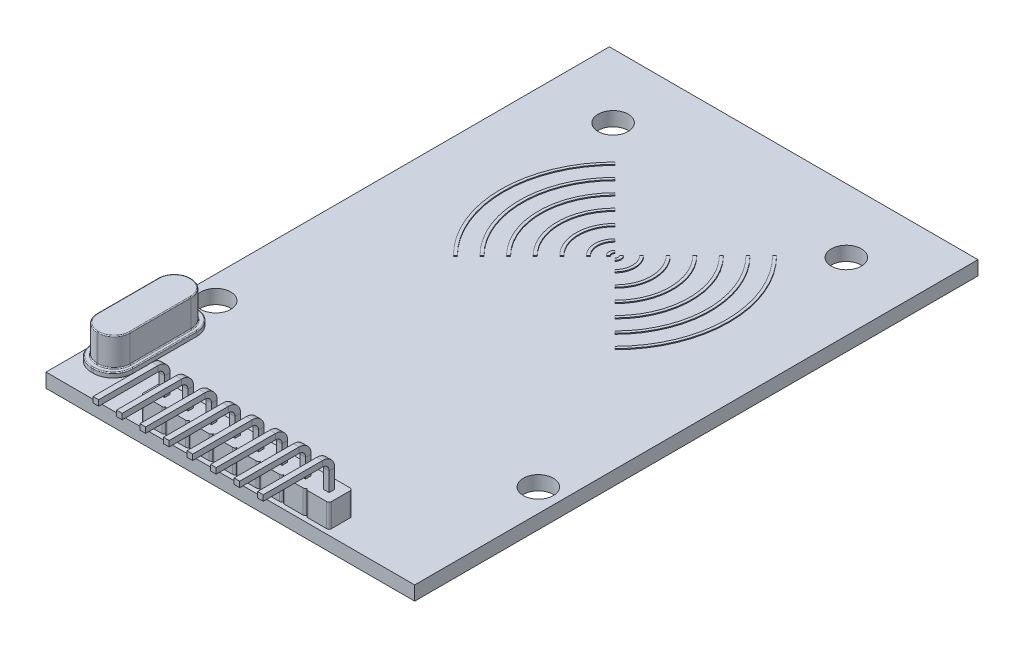
SolidWorks part; units mm, degrees
ref_plane "Front Plane" through (0, 0, 0) normal (0, 0, 1) x (1, 0, 0)
ref_plane "Top Plane" through (0, 0, 0) normal (0, 1, 0) x (1, 0, 0)
ref_plane "Right Plane" through (0, 0, 0) normal (1, 0, 0) x (0, 0, -1)
sketch "Sketch1" plane through (0, 0, 0) normal (0, 1, 0) x (1, 0, 0)
  line L1 (-19.6, 29.95) -> (19.6, 29.95)
  line L2 (-19.6, 29.95) -> (-19.6, -29.95)
  line L3 (-19.6, -29.95) -> (19.6, -29.95)
  line L4 (19.6, 29.95) -> (19.6, -29.95)
  line L5 (-19.6, 29.95) -> (19.6, -29.95) construction
  line L6 (-19.6, -29.95) -> (19.6, 29.95) construction
  point P0 (0, 0)
  dimension "D1" = 39.2
  dimension "D2" = 59.9
extrude "Boss-Extrude1" add sketch "Sketch1" along normal blind 1.5
sketch "Sketch3" plane through (0, 1.5, 0) normal (0, 1, 0) x (1, 0, 0)
  line L1 (-19.6, 29.95) -> (-19.6, -29.95) construction
  line L2 (19.6, 29.95) -> (-19.6, 29.95) construction
  line L5 (-19.6, -29.95) -> (19.6, -29.95) construction
  circle A0 centre (12.4, 23.15) radius 1.6
  circle A1 centre (-12.4, 23.15) radius 1.6
  circle A2 centre (17.15, -14.35) radius 1.6
  circle A3 centre (-17.15, -14.35) radius 1.6
  point P14 (0, 0)
  point P15 (0, 0)
  point P16 (0, 0)
  dimension "D1" = 3.2
  dimension "D2" = 24.8
  dimension "D3" = 6.8
  dimension "D4" = 7.2
  dimension "D5" = 6.8
  dimension "D6" = 34.3
  dimension "D7" = 2.45
  dimension "D8" = 15.6
  dimension "D9" = 15.6
extrude "Cut-Extrude1" cut sketch "Sketch3" against normal up to surface (1.5 mm away) up to face at (0, 0, 0)
sketch "Sketch4" plane through (0, 1.5, 0) normal (0, 1, 0) x (1, 0, 0)
  line L0 (-19.6, -29.95) -> (19.6, -29.95) construction
  line L1 (-9.75, -26.95) -> (-7.75, -26.95)
  line L2 (-10, -27.2) -> (-10, -29.2)
  line L3 (-9.75, -29.45) -> (-7.75, -29.45)
  line L5 (-19.6, 29.95) -> (-19.6, -29.95) construction
  line L7 (-7.25, -29.45) -> (-5.25, -29.45)
  line L9 (-7.25, -26.95) -> (-5.25, -26.95)
  line L11 (-4.75, -29.45) -> (-2.75, -29.45)
  line L13 (-4.75, -26.95) -> (-2.75, -26.95)
  line L15 (-2.25, -29.45) -> (-0.25, -29.45)
  line L17 (-2.25, -26.95) -> (-0.25, -26.95)
  line L19 (0.25, -29.45) -> (2.25, -29.45)
  line L21 (0.25, -26.95) -> (2.25, -26.95)
  line L23 (2.75, -29.45) -> (4.75, -29.45)
  line L25 (2.75, -26.95) -> (4.75, -26.95)
  line L27 (5.25, -29.45) -> (7.25, -29.45)
  line L29 (5.25, -26.95) -> (7.25, -26.95)
  line L30 (10, -27.2) -> (10, -29.2)
  line L31 (7.75, -29.45) -> (9.75, -29.45)
  line L33 (7.75, -26.95) -> (9.75, -26.95)
  line L34 (-7.5, -27.2) -> (-7.5, -29.2) [skipped]
  line L35 (-5, -27.2) -> (-5, -29.2) [skipped]
  line L36 (-2.5, -27.2) -> (-2.5, -29.2) [skipped]
  line L37 (0, -27.2) -> (0, -29.2) [skipped]
  line L38 (2.5, -27.2) -> (2.5, -29.2) [skipped]
  line L39 (5, -27.2) -> (5, -29.2) [skipped]
  line L40 (7.5, -27.2) -> (7.5, -29.2) [skipped]
  arc A1 (-7.75, -26.95) -> (-7.5, -27.2) centre (-7.75, -27.2) cw
  arc A2 (-7.5, -29.2) -> (-7.75, -29.45) centre (-7.75, -29.2) cw
  arc A3 (-9.75, -29.45) -> (-10, -29.2) centre (-9.75, -29.2) cw
  arc A4 (-10, -27.2) -> (-9.75, -26.95) centre (-9.75, -27.2) cw
  arc A5 (-5, -29.2) -> (-5.25, -29.45) centre (-5.25, -29.2) cw
  arc A6 (-7.25, -29.45) -> (-7.5, -29.2) centre (-7.25, -29.2) cw
  arc A7 (-7.5, -27.2) -> (-7.25, -26.95) centre (-7.25, -27.2) cw
  arc A8 (-5.25, -26.95) -> (-5, -27.2) centre (-5.25, -27.2) cw
  arc A10 (-2.5, -29.2) -> (-2.75, -29.45) centre (-2.75, -29.2) cw
  arc A11 (-4.75, -29.45) -> (-5, -29.2) centre (-4.75, -29.2) cw
  arc A12 (-5, -27.2) -> (-4.75, -26.95) centre (-4.75, -27.2) cw
  arc A13 (-2.75, -26.95) -> (-2.5, -27.2) centre (-2.75, -27.2) cw
  arc A15 (0, -29.2) -> (-0.25, -29.45) centre (-0.25, -29.2) cw
  arc A16 (-2.25, -29.45) -> (-2.5, -29.2) centre (-2.25, -29.2) cw
  arc A17 (-2.5, -27.2) -> (-2.25, -26.95) centre (-2.25, -27.2) cw
  arc A18 (-0.25, -26.95) -> (0, -27.2) centre (-0.25, -27.2) cw
  arc A20 (2.5, -29.2) -> (2.25, -29.45) centre (2.25, -29.2) cw
  arc A21 (0.25, -29.45) -> (0, -29.2) centre (0.25, -29.2) cw
  arc A22 (0, -27.2) -> (0.25, -26.95) centre (0.25, -27.2) cw
  arc A23 (2.25, -26.95) -> (2.5, -27.2) centre (2.25, -27.2) cw
  arc A25 (5, -29.2) -> (4.75, -29.45) centre (4.75, -29.2) cw
  arc A26 (2.75, -29.45) -> (2.5, -29.2) centre (2.75, -29.2) cw
  arc A27 (2.5, -27.2) -> (2.75, -26.95) centre (2.75, -27.2) cw
  arc A28 (4.75, -26.95) -> (5, -27.2) centre (4.75, -27.2) cw
  arc A30 (7.5, -29.2) -> (7.25, -29.45) centre (7.25, -29.2) cw
  arc A31 (5.25, -29.45) -> (5, -29.2) centre (5.25, -29.2) cw
  arc A32 (5, -27.2) -> (5.25, -26.95) centre (5.25, -27.2) cw
  arc A33 (7.25, -26.95) -> (7.5, -27.2) centre (7.25, -27.2) cw
  arc A35 (10, -29.2) -> (9.75, -29.45) centre (9.75, -29.2) cw
  arc A36 (7.75, -29.45) -> (7.5, -29.2) centre (7.75, -29.2) cw
  arc A37 (7.5, -27.2) -> (7.75, -26.95) centre (7.75, -27.2) cw
  arc A38 (9.75, -26.95) -> (10, -27.2) centre (9.75, -27.2) cw
  point P12 (-7.5, -26.95)
  point P17 (-10, -29.45)
  point P20 (-10, -26.95)
  dimension "D7" = 0.25
  dimension "D1" = 2.5
  dimension "D2" = 2.5
  dimension "D3" = 0.5
  dimension "D4" = 9.6
  dimension "D8" = 8
extrude "Boss-Extrude3" add sketch "Sketch4" along normal blind 2.5
sketch "Sketch5" plane through (0, 4, 0) normal (0, 1, 0) x (1, 0, 0)
  line L2 (-7.75, -26.95) -> (-9.75, -26.95) construction
  line L3 (-9.05, -27.9) -> (-8.45, -27.9)
  line L4 (-9.05, -27.9) -> (-9.05, -28.5)
  line L5 (-9.05, -28.5) -> (-8.45, -28.5)
  line L6 (-8.45, -27.9) -> (-8.45, -28.5)
  line L7 (-10, -27.2) -> (-10, -29.2) construction
  line L8 (-6.55, -27.9) -> (-5.95, -27.9)
  line L9 (-5.95, -27.9) -> (-5.95, -28.5)
  line L10 (-6.55, -28.5) -> (-5.95, -28.5)
  line L11 (-6.55, -27.9) -> (-6.55, -28.5)
  line L12 (-4.05, -27.9) -> (-3.45, -27.9)
  line L13 (-3.45, -27.9) -> (-3.45, -28.5)
  line L14 (-4.05, -28.5) -> (-3.45, -28.5)
  line L15 (-4.05, -27.9) -> (-4.05, -28.5)
  line L16 (-1.55, -27.9) -> (-0.95, -27.9)
  line L17 (-0.95, -27.9) -> (-0.95, -28.5)
  line L18 (-1.55, -28.5) -> (-0.95, -28.5)
  line L19 (-1.55, -27.9) -> (-1.55, -28.5)
  line L20 (0.95, -27.9) -> (1.55, -27.9)
  line L21 (1.55, -27.9) -> (1.55, -28.5)
  line L22 (0.95, -28.5) -> (1.55, -28.5)
  line L23 (0.95, -27.9) -> (0.95, -28.5)
  line L24 (3.45, -27.9) -> (4.05, -27.9)
  line L25 (4.05, -27.9) -> (4.05, -28.5)
  line L26 (3.45, -28.5) -> (4.05, -28.5)
  line L27 (3.45, -27.9) -> (3.45, -28.5)
  line L28 (5.95, -27.9) -> (6.55, -27.9)
  line L29 (6.55, -27.9) -> (6.55, -28.5)
  line L30 (5.95, -28.5) -> (6.55, -28.5)
  line L31 (5.95, -27.9) -> (5.95, -28.5)
  line L32 (8.45, -27.9) -> (9.05, -27.9)
  line L33 (9.05, -27.9) -> (9.05, -28.5)
  line L34 (8.45, -28.5) -> (9.05, -28.5)
  line L35 (8.45, -27.9) -> (8.45, -28.5)
  dimension "D1" = 0.6
  dimension "D2" = 0.6
  dimension "D3" = 0.95
  dimension "D4" = 0.95
  dimension "D5" = 8
extrude "Cut-Extrude2" cut sketch "Sketch5" against normal up to surface (4 mm away) up to face at (-17.15, 0, 15.95)
ref_plane "Plane1" through (0, -1, 0) normal (0, -1, 0) x (-1, 0, 0)
sketch "Sketch6" plane through (0, -1, 0) normal (0, -1, 0) x (-1, 0, 0)
  line L0 (6.55, -28.5) -> (5.95, -28.5)
  line L1 (9.05, -28.5) -> (8.45, -28.5)
  line L2 (9.05, -28.5) -> (9.05, -27.9)
  line L3 (9.05, -27.9) -> (8.45, -27.9)
  line L4 (8.45, -28.5) -> (8.45, -27.9)
  line L5 (5.95, -28.5) -> (5.95, -27.9)
  line L6 (6.55, -27.9) -> (5.95, -27.9)
  line L7 (6.55, -28.5) -> (6.55, -27.9)
  line L8 (4.05, -28.5) -> (3.45, -28.5)
  line L9 (3.45, -28.5) -> (3.45, -27.9)
  line L10 (4.05, -27.9) -> (3.45, -27.9)
  line L11 (4.05, -28.5) -> (4.05, -27.9)
  line L12 (1.55, -28.5) -> (0.95, -28.5)
  line L13 (0.95, -28.5) -> (0.95, -27.9)
  line L14 (1.55, -27.9) -> (0.95, -27.9)
  line L15 (1.55, -28.5) -> (1.55, -27.9)
  line L16 (-0.95, -28.5) -> (-1.55, -28.5)
  line L17 (-1.55, -28.5) -> (-1.55, -27.9)
  line L18 (-0.95, -27.9) -> (-1.55, -27.9)
  line L19 (-0.95, -28.5) -> (-0.95, -27.9)
  line L20 (-3.45, -28.5) -> (-4.05, -28.5)
  line L21 (-4.05, -28.5) -> (-4.05, -27.9)
  line L22 (-3.45, -27.9) -> (-4.05, -27.9)
  line L23 (-3.45, -28.5) -> (-3.45, -27.9)
  line L24 (-5.95, -28.5) -> (-6.55, -28.5)
  line L25 (-6.55, -28.5) -> (-6.55, -27.9)
  line L26 (-5.95, -27.9) -> (-6.55, -27.9)
  line L27 (-5.95, -28.5) -> (-5.95, -27.9)
  line L28 (-8.45, -28.5) -> (-9.05, -28.5)
  line L29 (-9.05, -28.5) -> (-9.05, -27.9)
  line L30 (-8.45, -27.9) -> (-9.05, -27.9)
  line L31 (-8.45, -28.5) -> (-8.45, -27.9)
  dimension "D1" = 8
sketch "Sketch7" plane through (-10, 0, 0) normal (-1, 0, 0) x (0, 0, 1)
  line L0 (28.2, -1) -> (28.2, 6)
  line L1 (28.5, -1) -> (27.9, -1) construction
  line L2 (29.2, 7) -> (35.5, 7)
  arc A0 (29.2, 7) -> (28.2, 6) centre (29.2, 6) ccw
  point P7 (28.2, 7)
  dimension "D3" = 1
  dimension "D1" = 7.3
  dimension "D2" = 8
sweep "Sweep1" add profiles "Sketch6" path "Sketch7"
sketch "Sketch8" plane through (0, 1.5, 0) normal (0, 1, 0) x (1, 0, 0)
  line L0 (-19.6, -29.95) -> (19.6, -29.95) construction
  line L1 (-17.16, -16.55) -> (-16.96, -16.55)
  line L2 (-19.26, -18.65) -> (-19.26, -25.45)
  line L3 (-17.16, -27.55) -> (-16.96, -27.55)
  line L4 (-14.86, -18.65) -> (-14.86, -25.45)
  arc A0 (-19.26, -25.45) -> (-17.16, -27.55) centre (-17.16, -25.45) ccw
  arc A1 (-16.96, -27.55) -> (-14.86, -25.45) centre (-16.96, -25.45) ccw
  arc A2 (-16.96, -16.55) -> (-14.86, -18.65) centre (-16.96, -18.65) cw
  arc A3 (-17.16, -16.55) -> (-19.26, -18.65) centre (-17.16, -18.65) ccw
  point P6 (-19.26, -27.55)
  point P11 (-14.86, -16.55)
  point P14 (-19.26, -16.55)
  dimension "D3" = 2.1
  dimension "D1" = 11
  dimension "D2" = 4.4
  dimension "D4" = 2.4
extrude "Boss-Extrude4" add sketch "Sketch8" along normal blind 0.5
sketch "Sketch10" plane through (0, 2, 0) normal (0, 1, 0) x (1, 0, 0)
  line L0 (-17.06, -16.55) -> (-17.06, -27.55) construction
  line L1 (-16.96, -16.55) -> (-17.16, -16.55) construction
  line L2 (-17.16, -27.55) -> (-16.96, -27.55) construction
  line L3 (-19.26, -22.05) -> (-14.86, -22.05) construction
  line L4 (-19.26, -18.65) -> (-19.26, -25.45) construction
  line L5 (-14.86, -25.45) -> (-14.86, -18.65) construction
  line L7 (-17.11, -17.1) -> (-17.01, -17.1)
  line L8 (-18.81, -18.8) -> (-18.81, -25.3)
  line L9 (-17.11, -27) -> (-17.01, -27)
  line L10 (-15.31, -18.8) -> (-15.31, -25.3)
  line L11 (-18.81, -17.1) -> (-15.31, -27) construction
  line L12 (-18.81, -27) -> (-15.31, -17.1) construction
  arc A0 (-18.81, -25.3) -> (-17.11, -27) centre (-17.11, -25.3) ccw
  arc A1 (-17.01, -27) -> (-15.31, -25.3) centre (-17.01, -25.3) ccw
  arc A2 (-15.31, -18.8) -> (-17.01, -17.1) centre (-17.01, -18.8) ccw
  arc A3 (-17.11, -17.1) -> (-18.81, -18.8) centre (-17.11, -18.8) ccw
  point P12 (-17.06, -22.05)
  dimension "D3" = 1.7
  dimension "D1" = 3.5
  dimension "D2" = 9.9
extrude "Boss-Extrude5" add sketch "Sketch10" along normal blind 3
fillet "Fillet1" radius 0.1 24 edges at (-18.3121, 5, 17.5979) (-17.06, 5, 17.1) (-15.8079, 5, 17.5979) (-15.31, 5, 22.05) (-15.8079, 5, 26.5021) (-17.06, 5, 27) (-18.3121, 5, 26.5021) (-18.3121, 2, 17.5979) (-17.06, 2, 17.1) (-15.8079, 2, 17.5979) (-15.31, 2, 22.05) (-15.8079, 2, 26.5021) (-17.06, 2, 27) (-18.3121, 2, 26.5021) (-18.6449, 2, 17.1651) (-17.06, 2, 16.55) (-15.4751, 2, 17.1651) (-14.86, 2, 22.05) (-15.4751, 2, 26.9349) (-17.06, 2, 27.55) (-18.6449, 2, 26.9349) (-18.81, 5, 22.05) (-18.81, 2, 22.05) (-19.26, 2, 22.05)
sketch "Sketch11" plane through (0, 1.5, 0) normal (0, 1, 0) x (1, 0, 0)
  line L0 (-0.2475, 11.1975) -> (-0.4596, 11.4096)
  line L1 (-0.35, 10.95) -> (-19.6, 10.95) construction
  line L2 (-19.6, 29.95) -> (-19.6, -29.95) construction
  line L3 (19.6, 29.95) -> (-19.6, 29.95) construction
  line L4 (0.2475, 11.1975) -> (0.4596, 11.4096)
  line L5 (-0.2475, 10.7025) -> (-0.4596, 10.4904)
  line L6 (0.2475, 10.7025) -> (0.4596, 10.4904)
  line L7 (-8.4853, 19.4353) -> (-8.5913, 19.5413)
  line L8 (-8.5913, 2.3587) -> (-8.4853, 2.4647)
  line L9 (8.4853, 2.4647) -> (8.5913, 2.3587)
  line L10 (8.4853, 19.4353) -> (8.5913, 19.5413)
  line L11 (-8.3792, 19.3292) -> (-8.4853, 19.4353)
  line L12 (-6.965, 17.915) -> (-7.1771, 18.1271)
  line L13 (-5.5508, 16.5008) -> (-5.7629, 16.7129)
  line L14 (-4.1366, 15.0866) -> (-4.3487, 15.2987)
  line L15 (-2.7224, 13.6724) -> (-2.9345, 13.8845)
  line L16 (-1.3081, 12.2581) -> (-1.5203, 12.4703)
  line L17 (-1.3081, 9.6419) -> (-1.5203, 9.4297)
  line L18 (-2.7224, 8.2276) -> (-2.9345, 8.0155)
  line L19 (-4.1366, 6.8134) -> (-4.3487, 6.6013)
  line L20 (-5.5508, 5.3992) -> (-5.7629, 5.1871)
  line L21 (-8.3792, 2.5708) -> (-8.4853, 2.4647)
  line L22 (1.3081, 9.6419) -> (1.5203, 9.4297)
  line L23 (2.7224, 8.2276) -> (2.9345, 8.0155)
  line L24 (4.1366, 6.8134) -> (4.3487, 6.6013)
  line L25 (5.5508, 5.3992) -> (5.7629, 5.1871)
  line L26 (6.965, 3.985) -> (7.1771, 3.7729)
  line L27 (8.3792, 2.5708) -> (8.4853, 2.4647)
  line L28 (1.3081, 12.2581) -> (1.5203, 12.4703)
  line L29 (2.7224, 13.6724) -> (2.9345, 13.8845)
  line L30 (4.1366, 15.0866) -> (4.3487, 15.2987)
  line L31 (5.5508, 16.5008) -> (5.7629, 16.7129)
  line L32 (6.965, 17.915) -> (7.1771, 18.1271)
  line L33 (8.3792, 19.3292) -> (8.4853, 19.4353)
  line L34 (-6.965, 3.985) -> (-7.1771, 3.7729)
  arc A0 (-0.3536, 11.3036) -> (-0.3536, 10.5964) centre (0, 10.95) ccw construction
  arc A1 (-1.4142, 12.3642) -> (-1.4142, 9.5358) centre (0, 10.95) ccw construction
  arc A2 (-2.8284, 13.7784) -> (-2.8284, 8.1216) centre (0, 10.95) ccw construction
  arc A3 (-4.2426, 15.1926) -> (-4.2426, 6.7074) centre (0, 10.95) ccw construction
  arc A4 (-5.6569, 16.6069) -> (-5.6569, 5.2931) centre (0, 10.95) ccw construction
  arc A5 (-5.6569, 16.6069) -> (-5.6569, 5.2931) centre (0, 10.95) ccw
  arc A6 (-7.0711, 18.0211) -> (-7.0711, 3.8789) centre (0, 10.95) ccw construction
  arc A7 (-8.4853, 19.4353) -> (-8.4853, 2.4647) centre (0, 10.95) ccw construction
  arc A8 (0.3536, 10.5964) -> (0.3536, 11.3036) centre (0, 10.95) ccw construction
  arc A9 (1.4142, 9.5358) -> (1.4142, 12.3642) centre (0, 10.95) ccw construction
  arc A10 (2.8284, 8.1216) -> (2.8284, 13.7784) centre (0, 10.95) ccw construction
  arc A11 (4.2426, 6.7074) -> (4.2426, 15.1926) centre (0, 10.95) ccw construction
  arc A12 (5.6569, 5.2931) -> (5.6569, 16.6069) centre (0, 10.95) ccw construction
  arc A13 (5.6569, 5.2931) -> (5.6569, 16.6069) centre (0, 10.95) ccw
  arc A14 (7.0711, 3.8789) -> (7.0711, 18.0211) centre (0, 10.95) ccw construction
  arc A15 (8.4853, 2.4647) -> (8.4853, 19.4353) centre (0, 10.95) ccw construction
  arc A16 (-8.5913, 19.5413) -> (-8.5913, 2.3587) centre (0, 10.95) ccw
  arc A17 (-7.1771, 18.1271) -> (-7.1771, 3.7729) centre (0, 10.95) ccw
  arc A18 (-5.7629, 16.7129) -> (-5.7629, 5.1871) centre (0, 10.95) ccw
  arc A19 (-4.3487, 15.2987) -> (-4.3487, 6.6013) centre (0, 10.95) ccw
  arc A20 (-2.9345, 13.8845) -> (-2.9345, 8.0155) centre (0, 10.95) ccw
  arc A21 (-1.5203, 12.4703) -> (-1.5203, 9.4297) centre (0, 10.95) ccw
  arc A22 (-0.4596, 11.4096) -> (-0.4596, 10.4904) centre (0, 10.95) ccw
  arc A23 (0.4596, 10.4904) -> (0.4596, 11.4096) centre (0, 10.95) ccw
  arc A24 (1.5203, 9.4297) -> (1.5203, 12.4703) centre (0, 10.95) ccw
  arc A25 (2.9345, 8.0155) -> (2.9345, 13.8845) centre (0, 10.95) ccw
  arc A26 (4.3487, 6.6013) -> (4.3487, 15.2987) centre (0, 10.95) ccw
  arc A27 (5.7629, 5.1871) -> (5.7629, 16.7129) centre (0, 10.95) ccw
  arc A28 (7.1771, 3.7729) -> (7.1771, 18.1271) centre (0, 10.95) ccw
  arc A29 (8.5913, 2.3587) -> (8.5913, 19.5413) centre (0, 10.95) ccw
  arc A30 (-8.3792, 19.3292) -> (-8.3792, 2.5708) centre (0, 10.95) ccw
  arc A31 (-6.965, 17.915) -> (-6.965, 3.985) centre (0, 10.95) ccw
  arc A32 (-5.5508, 16.5008) -> (-5.5508, 5.3992) centre (0, 10.95) ccw
  arc A33 (-4.1366, 15.0866) -> (-4.1366, 6.8134) centre (0, 10.95) ccw
  arc A34 (-2.7224, 13.6724) -> (-2.7224, 8.2276) centre (0, 10.95) ccw
  arc A35 (-1.3081, 12.2581) -> (-1.3081, 9.6419) centre (0, 10.95) ccw
  arc A36 (-0.2475, 11.1975) -> (-0.2475, 10.7025) centre (0, 10.95) ccw
  arc A37 (0.2475, 10.7025) -> (0.2475, 11.1975) centre (0, 10.95) ccw
  arc A38 (1.3081, 9.6419) -> (1.3081, 12.2581) centre (0, 10.95) ccw
  arc A39 (2.7224, 8.2276) -> (2.7224, 13.6724) centre (0, 10.95) ccw
  arc A40 (4.1366, 6.8134) -> (4.1366, 15.0866) centre (0, 10.95) ccw
  arc A41 (5.5508, 5.3992) -> (5.5508, 16.5008) centre (0, 10.95) ccw
  arc A42 (6.965, 3.985) -> (6.965, 17.915) centre (0, 10.95) ccw
  arc A43 (8.3792, 2.5708) -> (8.3792, 19.3292) centre (0, 10.95) ccw
  dimension "D1" = 45
  dimension "D2" = 0.5
  dimension "D3" = 2
  dimension "D4" = 6
  dimension "D5" = 10
  dimension "D6" = 19
  dimension "D10" = 8
  dimension "D11" = 4
  dimension "D12" = 12
  dimension "D7" = 45
  dimension "D8" = 45
  dimension "D9" = 45
  dimension "D13" = 0.15
  dimension "D14" = 0.15
extrude "Boss-Extrude6" add sketch "Sketch11" along normal blind 0.1 contours A16 L8 L21 A30 L11 L7 | A17 L34 A31 L12 | A18 L20 A32 L13 | A19 L19 A33 L14 | A20 L18 A34 L15 | A35 L17 A21 L16 | A36 L5 A22 L0 | A23 L4 A37 L6 | A24 L28 A38 L22 | A25 L29 A39 L23 | A26 L30 A40 L24 | A27 L31 A41 L25 | A28 L32 A42 L26 | A29 L10 L33 A43 L27 L9
